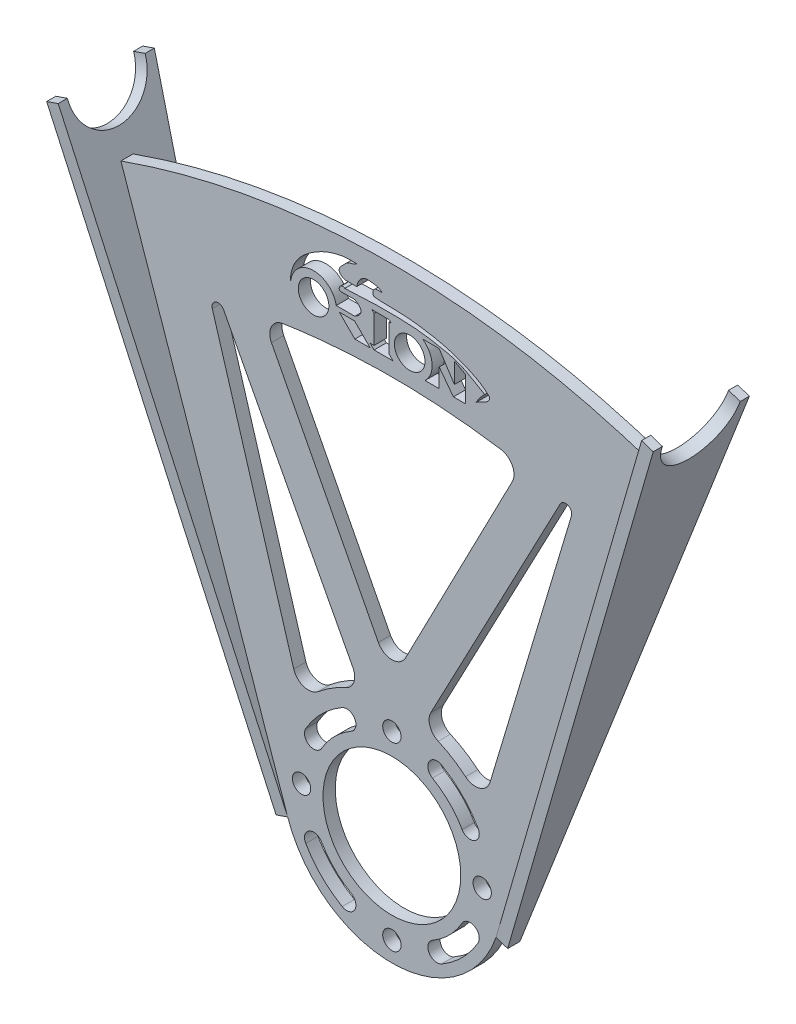
SolidWorks part; units mm, degrees
material "AISI 1020"
ref_plane "Front Plane" through (0, 0, 0) normal (0, 0, 1) x (1, 0, 0)
ref_plane "Top Plane" through (0, 0, 0) normal (0, 1, 0) x (1, 0, 0)
ref_plane "Right Plane" through (0, 0, 0) normal (1, 0, 0) x (0, 0, -1)
sketch "Sketch1" plane through (0, 0, 0) normal (0, 0, 1) x (1, 0, 0)
  line L0 (0, 0) -> (0, 180) construction
  line L1 (-100, 180) -> (-34.0416, -11.712)
  line L2 (-100, 180) -> (-80, 180)
  line L3 (100, 180) -> (34.0416, -11.712)
  line L4 (-15.3826, 149.6126) -> (-11.4915, 149.6126)
  line L5 (-80, 180) -> (-77.1604, 171.7467)
  line L6 (-67.7045, 165) -> (67.7045, 165)
  line L7 (-80, 180) -> (-68.9011, 147.7405) construction
  line L8 (39.408, 120) -> (-39.408, 120)
  line L9 (24.064, 135.141) -> (-22.7617, 153.8713) construction
  line L10 (9.6533, 148.6279) -> (-25.5076, 134.5636) construction
  line L11 (-16.2163, 145.6198) -> (-12.0945, 145.6198)
  line L12 (-18.1799, 140.9184) -> (-12.0945, 140.9184)
  line L13 (-17.1816, 139.563) -> (-12.0945, 134.4759)
  line L14 (-12.0945, 134.4759) -> (-7.0941, 134.4759)
  line L15 (-7.0941, 134.4759) -> (-12.1812, 139.563)
  line L16 (-12.1812, 139.563) -> (-17.1816, 139.563)
  line L17 (-6.5194, 145.6198) -> (-5.8174, 144.9178)
  line L18 (-5.8174, 144.9178) -> (-5.8174, 135.8049)
  line L19 (-5.8174, 135.8049) -> (-7.0941, 135.8049)
  line L20 (-7.0941, 135.8049) -> (-5.8174, 134.5282)
  line L21 (-5.8174, 134.5282) -> (0.3955, 134.5282)
  line L22 (0.3955, 134.5282) -> (-0.8812, 135.8049)
  line L23 (-0.8812, 135.8049) -> (-0.8812, 144.9178)
  line L24 (-0.8812, 144.9178) -> (-0.2428, 144.9178)
  line L25 (-0.2428, 144.9178) -> (-0.8812, 145.5561)
  line L26 (-0.8812, 145.5561) -> (-6.5194, 145.6198)
  line L27 (10.0461, 145.5561) -> (15.4497, 145.5561)
  line L28 (15.4497, 145.5561) -> (20.4259, 137.881)
  line L29 (20.4259, 137.881) -> (20.4259, 144.5342)
  line L30 (20.4259, 144.5342) -> (24.064, 142.5379)
  line L31 (24.064, 142.5379) -> (24.064, 134.2169)
  line L32 (24.064, 134.2169) -> (20.0914, 134.2169)
  line L33 (20.0914, 134.2169) -> (15.4497, 140.364)
  line L34 (15.4497, 140.364) -> (15.4497, 134.2169)
  line L35 (15.4497, 134.2169) -> (10.8398, 134.2169)
  line L36 (-58.6711, 119.8424) -> (-32.0695, 31.1524)
  line L37 (58.6711, 119.8424) -> (32.0695, 31.1524)
  line L38 (-39.408, 120) -> (-4.4395, 52.5056)
  line L39 (-54.9863, 121.3498) -> (-12.7342, 41.215)
  line L40 (54.9863, 121.3498) -> (12.7342, 41.215)
  line L41 (39.408, 120) -> (4.4395, 52.5056)
  line L42 (-54.3759, 105.522) -> (-28.0236, 28.9275) construction
  line L43 (80, 180) -> (77.1604, 171.7467)
  line L44 (80, 180) -> (100, 180)
  circle A0 centre (0, 0) radius 22.5
  circle A5 centre (-29.5, 0) radius 3
  arc A6 (-34.0416, -11.712) -> (34.0416, -11.712) centre (0, 0) ccw
  circle A7 centre (-25.5831, 139.563) radius 5
  circle A8 centre (5.821, 139.563) radius 5
  arc A9 (-18.1799, 140.9184) -> (-33.1094, 139.563) centre (-25.5831, 139.563) ccw
  arc A10 (10.8398, 134.2169) -> (10.0461, 145.5561) centre (5.821, 139.563) ccw
  arc A11 (-77.1604, 171.7467) -> (-67.7045, 165) centre (-67.7045, 175) ccw
  arc A12 (-15.1386, 34.3085) -> (-24.0708, 28.7549) centre (0, 0) ccw
  circle A13 centre (0, 0) radius 37.5 construction
  arc A14 (15.1386, 34.3085) -> (24.0708, 28.7549) centre (0, 0) cw
  arc A15 (77.1604, 171.7467) -> (67.7045, 165) centre (67.7045, 175) cw
  arc A16 (-58.6711, 119.8424) -> (-54.9863, 121.3498) centre (-56.7555, 120.417) cw
  arc A17 (58.6711, 119.8424) -> (54.9863, 121.3498) centre (56.7555, 120.417) ccw
  arc A18 (-32.0695, 31.1524) -> (-24.0708, 28.7549) centre (-27.2803, 32.5889) ccw
  arc A19 (-12.7342, 41.215) -> (-15.1386, 34.3085) centre (-17.157, 38.883) cw
  arc A20 (24.0708, 28.7549) -> (32.0695, 31.1524) centre (27.2803, 32.5889) ccw
  arc A21 (15.1386, 34.3085) -> (12.7342, 41.215) centre (17.157, 38.883) cw
  arc A22 (-4.4395, 52.5056) -> (4.4395, 52.5056) centre (0, 54.8057) ccw
  arc A23 (-28.1458, 16.25) -> (-22.9497, 13.25) centre (-25.5477, 14.75) ccw
  arc A24 (-13.25, 22.9497) -> (-16.25, 28.1458) centre (-14.75, 25.5477) ccw
  circle A25 centre (0, 29.5) radius 3
  arc A26 (16.25, 28.1458) -> (13.25, 22.9497) centre (14.75, 25.5477) ccw
  arc A27 (22.9497, 13.25) -> (28.1458, 16.25) centre (25.5477, 14.75) ccw
  circle A28 centre (29.5, 0) radius 3
  arc A29 (28.1458, -16.25) -> (22.9497, -13.25) centre (25.5477, -14.75) ccw
  arc A30 (13.25, -22.9497) -> (16.25, -28.1458) centre (14.75, -25.5477) ccw
  circle A31 centre (0, -29.5) radius 3
  arc A32 (-16.25, -28.1458) -> (-13.25, -22.9497) centre (-14.75, -25.5477) ccw
  arc A33 (-22.9497, -13.25) -> (-28.1458, -16.25) centre (-25.5477, -14.75) ccw
  arc A34 (-13.25, 22.9497) -> (-22.9497, 13.25) centre (0, 0) ccw
  arc A35 (-16.25, 28.1458) -> (-28.1458, 16.25) centre (0, 0) ccw
  arc A36 (2.9961, 29.3475) -> (-2.9961, 29.3475) centre (0, 0) ccw construction
  arc A37 (22.9497, 13.25) -> (13.25, 22.9497) centre (0, 0) ccw
  arc A38 (23.9176, 17.2684) -> (17.2684, 23.9176) centre (0, 0) ccw construction
  arc A39 (28.1458, 16.25) -> (16.25, 28.1458) centre (0, 0) ccw
  arc A40 (29.3475, -2.9961) -> (29.3475, 2.9961) centre (0, 0) ccw construction
  arc A41 (-22.9497, -13.25) -> (-13.25, -22.9497) centre (0, 0) ccw
  arc A42 (-29.3475, 2.9961) -> (-29.3475, -2.9961) centre (0, 0) ccw construction
  arc A43 (-28.1458, -16.25) -> (-16.25, -28.1458) centre (0, 0) ccw
  arc A45 (13.25, -22.9497) -> (22.9497, -13.25) centre (0, 0) ccw
  arc A46 (-2.9961, -29.3475) -> (2.9961, -29.3475) centre (0, 0) ccw construction
  arc A47 (16.25, -28.1458) -> (28.1458, -16.25) centre (0, 0) ccw
  spline S0 degree 3 poles (-33.1094, 139.563) (-33.3484, 142.6673) (-31.6807, 147.5835) (-26.6795, 151.7559) (-20.536, 155.2629) (-15.2202, 156.401) (-11.4915, 156.0703) knots 0 0 0 0 0.301465 0.480013 0.632553 1 1 1 1
  spline S1 degree 3 poles (-11.4915, 156.0703) (-12.4242, 155.3104) (-14.5876, 155.317) (-15.8626, 153.4059) (-17.0139, 152.5359) (-17.5474, 150.6848) (-16.0588, 149.8472) (-15.3826, 149.6126) knots 0 0 0 0 0.349428 0.525829 0.632453 0.767129 1 1 1 1
  spline S2 degree 3 poles (-11.4915, 149.6126) (-11.2798, 150.6434) (-10.672, 152.3737) (-8.4641, 153.4995) (-5.9842, 153.2565) (-4.1184, 152.9916) (-3.1847, 152.1136) knots 0 0 0 0 0.307613 0.470619 0.661138 1 1 1 1
  spline S3 degree 3 poles (-3.1847, 152.1136) (-3.8372, 151.9522) (-6.1496, 152.5809) (-6.3915, 150.1491) (-5.8174, 149.6126) knots 0 0 0 0 0.52143 1 1 1 1
  spline S4 degree 3 poles (-5.8174, 149.6126) (-2.8573, 149.2528) (1.7225, 149.4515) (7.8784, 148.9228) (12.6296, 148.1743) (17.4009, 147.27) (24.0835, 144.908) (29.1704, 142.8374) (31.9609, 140.0035) knots 0 0 0 0 0.224335 0.345082 0.465663 0.587504 0.710743 1 1 1 1
  spline S5 degree 3 poles (31.9609, 140.0035) (32.0282, 138.9209) (30.2113, 137.6395) (28.3676, 137.1081) (27.5144, 136.3784) knots 0 0 0 0 0.470544 1 1 1 1
  spline S6 degree 2 poles (27.5144, 136.3784) (28.6462, 138.3904) (30.3124, 140.0035) knots 0 0 0 1 1 1
  spline S7 degree 3 poles (-15.3826, 147.1555) (-11.1922, 147.4109) (-5.0315, 147.7152) (3.3519, 147.6288) (9.7585, 147.2992) (16.0531, 146.1476) (23.2902, 144.5793) (27.5488, 141.4564) (30.3124, 140.0035) knots 0 0 0 0 0.267114 0.391846 0.533351 0.674067 0.799249 1 1 1 1
  spline S8 degree 3 poles (-15.3826, 147.1555) (-16.9525, 148.3395) (-18.1128, 145.2597) (-16.2163, 145.6198) knots 0 0 0 0 1 1 1 1
  spline S9 degree 2 poles (-12.0945, 145.6198) (-8.0523, 143.2907) (-12.0945, 140.9184) knots 0 0 0 1 1 1
  point P7 (0, 144.7666)
  point P125 (0, 120)
  point P126 (0, 165)
  point P130 (-64.5817, 139.5484)
  point P133 (64.5817, 139.5484)
  point P136 (-29.6226, 22.9946)
  point P139 (-10.0518, 36.1277)
  point P142 (29.6226, 22.9946)
  point P145 (10.0518, 36.1277)
  point P148 (0, 43.9366)
  point P174 (0, 0)
  dimension "D1" = 45
  dimension "D4" = 72
  dimension "D6" = 200
  dimension "D7" = 36
  dimension "D10" = 15
  dimension "D11" = 60
  dimension "D8" = 10
  dimension "D13" = 2
  dimension "D14" = 2
  dimension "D15" = 5
  dimension "D5" = 180
  dimension "D9" = 20
  dimension "D12" = 15
  dimension "D16" = 12
extrude "Boss-Extrude1" add sketch "Sketch1" along normal blind 4
sketch "Sketch4" plane through (0, 180, 0) normal (0, 1, 0) x (1, 0, 0)
  line L0 (-80, 0) -> (-100, 0) construction
  line L2 (-90, -4) -> (-90, 0) construction
  line L4 (-80, -4) -> (-100, -4) construction
  point P0 (-90, -2)
sketch "Sketch8" plane through (0, 0, 4) normal (0, 0, 1) x (1, 0, 0)
  line L0 (-200.9399, 66.505) -> (-195.8581, 212.7286)
  line L1 (-195.8581, 212.7286) -> (191.9399, 202.2971)
  line L2 (191.9399, 202.2971) -> (200.9399, 66.505)
  spline S1 degree 3 poles (200.9399, 66.505) (198.086, 70.1684) (192.1679, 77.3127) (179.4127, 90.9706) (161.8779, 106.6989) (138.5566, 123.1701) (104.8565, 141.6026) (58.7101, 157.4964) (0, 163.9817) (-58.7101, 157.4964) (-104.8565, 141.6026) (-138.5566, 123.1701) (-161.8779, 106.6989) (-179.4127, 90.9706) (-192.1679, 77.3127) (-198.086, 70.1684) (-200.9399, 66.505) knots 0.628759 0.628759 0.628759 0.628759 0.687636 0.746514 0.864268 0.982023 1.099778 1.335287 1.570796 1.806306 2.041815 2.15957 2.277324 2.395079 2.453956 2.512834 2.512834 2.512834 2.512834
extrude "Cut-Extrude1" cut sketch "Sketch8" against normal blind 10
sketch "Sketch11" plane through (-34.0416, -11.712, 0) normal (-0.9456, -0.3253, 0) x (0, 0, 1)
  line L0 (4, 167.4676) -> (0, 167.4676) construction
  line L2 (0, 0) -> (-13.7, 188.2976)
  line L3 (4, 0) -> (17.7, 188.2976)
  line L4 (-10.7, 188.2976) -> (-13.7, 188.2976)
  line L5 (14.7, 188.2976) -> (17.7, 188.2976)
  line L6 (2, 175.5976) -> (2, -90.8541) construction
  line L10 (4, 0) -> (4, 167.4676)
  line L11 (4, 167.4676) -> (0, 167.4676)
  line L12 (0, 167.4676) -> (0, 0)
  line L13 (0, 0) -> (4, 0)
  line L17 (0, 0) -> (4, 0)
  arc A0 (-10.7, 188.2976) -> (14.7, 188.2976) centre (2, 188.2976) ccw
  dimension "D1" = 25.4
  dimension "D2" = 20.83
  dimension "D3" = 3
  dimension "D4" = 3
  dimension "D5" = 0
extrude "Boss-Extrude2" add sketch "Sketch11" along normal blind 4
mirror "Mirror1" about plane through (0, 0, 0) normal (1, 0, 0) of "Boss-Extrude2"
sketch "Sketch13" plane through (0, 0, 0) normal (1, 0, 0) x (0, 0, -1)
  line L0 (-2, 190.0236) -> (-2, 0.1292) construction
sketch "Sketch14" plane through (-37.824, -13.0133, 0) normal (-0.9456, -0.3253, 0) x (0, 0, 1)
  circle A0 centre (2, 188.2976) radius 12.7
sketch "Sketch15" plane through (37.824, -13.0133, 0) normal (0.9456, -0.3253, 0) x (0, 0, -1)
  circle A0 centre (-2, 188.2976) radius 12.7
sketch "Sketch16" plane through (0, 0, 4) normal (0, 0, 1) x (1, 0, 0)
  line L0 (4.4395, 52.5056) -> (39.408, 120) construction
  line L1 (-39.408, 120) -> (-42.4865, 125.9418)
  line L2 (39.408, 120) -> (42.4865, 125.9418)
  line L3 (-39.408, 120) -> (39.408, 120)
  line L4 (-39.408, 120) -> (-4.4395, 52.5056) construction
  spline S2 degree 3 poles (2697.3368, -677.3711) (-470.6141, -614.9184) (-355.159, 44.9885) (-52.6023, 123.9409) (-46.1438, 125.3337) (-26.5717, 128.6871) (-13.2755, 129.82) (13.2755, 129.82) (26.5717, 128.6871) (46.1438, 125.3337) (52.6023, 123.9409) (355.1584, 44.9887) (470.6137, -614.916) (-2697.319, -677.3708) knots -5.681751 -5.681751 -5.681751 -5.681751 0.125 0.125 0.25 0.25 0.5 0.5 0.75 0.75 0.875 0.875 6.68174 6.68174 6.68174 6.68174 only from (-77.8232, 116.4876) to (77.8232, 116.4876)
  spline S3 degree 3 poles (-42.4865, 125.9418) (-41.5324, 126.1176) (-40.5768, 126.2875) (-26.5717, 128.6871) (-13.2755, 129.82) (13.2755, 129.82) (26.5717, 128.6871) (40.5768, 126.2875) (41.5324, 126.1176) (42.4865, 125.9418) knots 0.231664 0.231664 0.231664 0.231664 0.25 0.25 0.5 0.5 0.75 0.75 0.768336 0.768336 0.768336 0.768336
  dimension "D1" = 32
extrude "Cut-Extrude3" cut sketch "Sketch16" against normal blind 4
fillet "Fillet6" radius 5 1 edges
fillet "Fillet7" radius 5 1 edges
